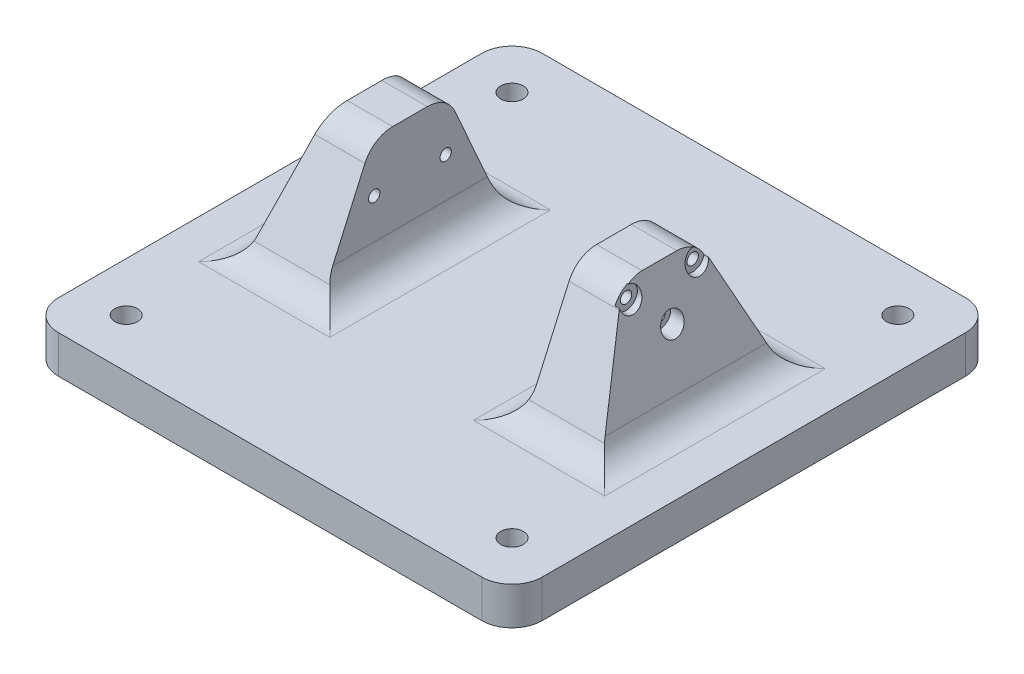
SolidWorks part; units mm, degrees
ref_plane "Front Plane" through (0, 0, 0) normal (0, 0, 1) x (1, 0, 0)
ref_plane "Top Plane" through (0, 0, 0) normal (0, 1, 0) x (1, 0, 0)
ref_plane "Right Plane" through (0, 0, 0) normal (1, 0, 0) x (0, 0, -1)
sketch "Sketch1" plane through (0, 0, 0) normal (0, 1, 0) x (1, 0, 0)
  line L1 (0, 0) -> (101.6, 0)
  line L2 (0, 0) -> (0, 101.6)
  line L3 (0, 101.6) -> (101.6, 101.6)
  line L4 (101.6, 0) -> (101.6, 101.6)
  dimension "D1" = 101.6
extrude "Boss-Extrude1" add sketch "Sketch1" along normal blind 7.9375
ref_plane "Plane1" through (50.8, 0, 0) normal (-1, 0, 0) x (0, 0, 1)
ref_plane "Plane2" through (29.3687, 0, 0) normal (-1, 0, 0) x (0, 0, 1)
sketch "Sketch2" plane through (29.3687, 0, 0) normal (-1, 0, 0) x (0, 0, 1)
  line L0 (-101.6, 7.9375) -> (0, 7.9375) construction
  line L1 (-101.6, 7.9375) -> (0, 7.9375) construction
  line L2 (-31.75, 7.9375) -> (-69.85, 7.9375)
  line L3 (-69.85, 7.9375) -> (-58.5788, 33.3375)
  line L4 (-58.5788, 33.3375) -> (-43.0213, 33.3375)
  line L5 (-43.0213, 33.3375) -> (-31.75, 7.9375)
  point P6 (-50.8, 7.9375)
  point P8 (-50.8, 7.9375)
  point P9 (-50.8, 33.3375)
  dimension "D1" = 38.1
  dimension "D2" = 15.5575
  dimension "D3" = 25.4
extrude "Boss-Extrude2" add sketch "Sketch2" along normal blind 9.525
draft "Draft2" type of draft neutral plane draft angle 15 faces to draft 1 face at (19.8438, 20.6375, -50.8) neutral plane through (19.8438, 33.3375, -58.5788) neutral plane normal (0, 1, 0) parameters "D1"=15
mirror "Mirror2" about plane through (50.8, 0, 0) normal (-1, 0, 0) of "Boss-Extrude2"
draft "Draft3" type of draft neutral plane draft angle 15 faces to draft 1 face at (81.7563, 20.6375, -50.8) neutral plane through (81.7563, 33.3375, -58.5788) neutral plane normal (0, 1, 0) parameters "D1"=15
fillet "Fillet3" radius 6.35 12 edges at (13.0378, 7.9375, -50.8) (88.5622, 7.9375, -50.8) (80.3967, 7.9375, -69.85) (21.2033, 7.9375, -69.85) (24.6062, 33.3375, -58.5788) (24.6062, 33.3375, -43.0213) (21.2033, 7.9375, -31.75) (76.9938, 33.3375, -58.5788) (76.9938, 33.3375, -43.0213) (80.3967, 7.9375, -31.75) (29.3687, 7.9375, -50.8) (72.2313, 7.9375, -50.8)
sketch "Sketch3" plane through (72.2313, 0, 0) normal (-1, 0, 0) x (0, 0, 1)
  line L0 (-47.1506, 33.3375) -> (-54.4494, 33.3375) construction
  line L1 (-47.1506, 33.3375) -> (-54.4494, 33.3375) construction
  line L2 (-57.8, 30.1625) -> (-43.8, 30.1625) construction
  circle A0 centre (-57.8, 30.1625) radius 1.1906
  circle A1 centre (-43.8, 30.1625) radius 1.1906
  circle A2 centre (-50.8, 23.1625) radius 1.1906
  point P4 (-50.8, 33.3375)
  point P5 (-50.8, 30.1625)
  dimension "D3" = 2.3813
  dimension "D1" = 3.175
  dimension "D2" = 14
  dimension "D4" = 7
extrude "Cut-Extrude1" cut sketch "Sketch3" against normal up to surface (10.3757 mm away)
ref_plane "Plane3" through (81.7563, 0, 0) normal (-1, 0, 0) x (0, 0, 1)
sketch "Sketch4" plane through (81.7563, 0, 0) normal (-1, 0, 0) x (0, 0, 1)
  circle A0 centre (-57.8, 30.1625) radius 1.1906 construction
  circle A1 centre (-43.8, 30.1625) radius 1.1906 construction
  circle A2 centre (-57.8, 30.1625) radius 1.1906 construction
  circle A3 centre (-43.8, 30.1625) radius 1.1906 construction
  circle A4 centre (-43.8, 30.1625) radius 2.3812
  circle A5 centre (-57.8, 30.1625) radius 2.3812
  circle A6 centre (-50.8, 23.1625) radius 1.1906 construction
  circle A7 centre (-50.8, 23.1625) radius 1.1906 construction
  circle A8 centre (-50.8, 23.1625) radius 2.3812
  dimension "D1" = 4.7625
extrude "Cut-Extrude2" cut sketch "Sketch4" against normal blind 6.35
sketch "Sketch5" plane through (0, 7.9375, 0) normal (0, 1, 0) x (1, 0, 0)
  line L0 (0, 101.6) -> (0, 0) construction
  line L1 (0, 101.6) -> (0, 0) construction
  line L2 (0, 0) -> (101.6, 0) construction
  line L3 (101.6, 101.6) -> (0, 101.6) construction
  line L4 (0, 0) -> (101.6, 0) construction
  line L5 (101.6, 101.6) -> (0, 101.6) construction
  line L6 (10.287, 101.6) -> (10.287, 0) construction
  line L7 (50.8, 101.6) -> (50.8, 0) construction
  circle A0 centre (10.287, 91.313) radius 2.3812
  circle A1 centre (10.287, 10.287) radius 2.3813
  circle A2 centre (91.313, 10.287) radius 2.3812
  circle A3 centre (91.313, 91.313) radius 2.3812
  dimension "D2" = 4.7625
  dimension "D1" = 10.287
  dimension "D3" = 10.287
  dimension "D4" = 10.287
extrude "Cut-Extrude3" cut sketch "Sketch5" against normal up to surface (7.9375 mm away) up to face at (50.8, 0, -50.8)
sketch "Sketch6" plane through (29.3687, 0, 0) normal (1, 0, 0) x (0, 0, -1)
  line L0 (47.1506, 33.3375) -> (54.4494, 33.3375) construction
  line L1 (47.1506, 33.3375) -> (54.4494, 33.3375) construction
  line L2 (50.8, 30.1625) -> (50.8, 33.3375) construction
  line L3 (47.1506, 30.1625) -> (54.4494, 30.1625) construction
  line L4 (43.3, 22.6625) -> (58.3, 22.6625) construction
  circle A0 centre (43.3, 22.6625) radius 1.1906
  circle A2 centre (58.3, 22.6625) radius 1.1906
  point P5 (50.8, 33.3375)
  point P10 (50.8, 30.1625)
  point P13 (50.8, 22.6625)
  dimension "D3" = 2.3813
  dimension "D1" = 3.175
  dimension "D2" = 15
  dimension "D4" = 7.5
extrude "Cut-Extrude4" cut sketch "Sketch6" against normal up to surface (12.3854 mm away)
ref_plane "Plane4" through (19.8438, 0, 0) normal (1, 0, 0) x (0, 0, -1)
sketch "Sketch7" plane through (19.8438, 0, 0) normal (1, 0, 0) x (0, 0, -1)
  circle A4 centre (58.3, 22.6625) radius 2.3812
  circle A5 centre (43.3, 22.6625) radius 2.3812
  circle A6 centre (43.3, 22.6625) radius 1.1906 construction
  circle A7 centre (58.3, 22.6625) radius 1.1906 construction
  circle A8 centre (43.3, 22.6625) radius 1.1906
  circle A9 centre (58.3, 22.6625) radius 1.1906
  dimension "D1" = 4.7625
extrude "Cut-Extrude5" cut sketch "Sketch7" against normal up to surface (2.8604 mm away)
fillet "Fillet4" radius 6.35 4 edges at (0, 3.9688, -101.6) (101.6, 3.9688, -101.6) (101.6, 3.9688, 0) (0, 3.9688, 0)
